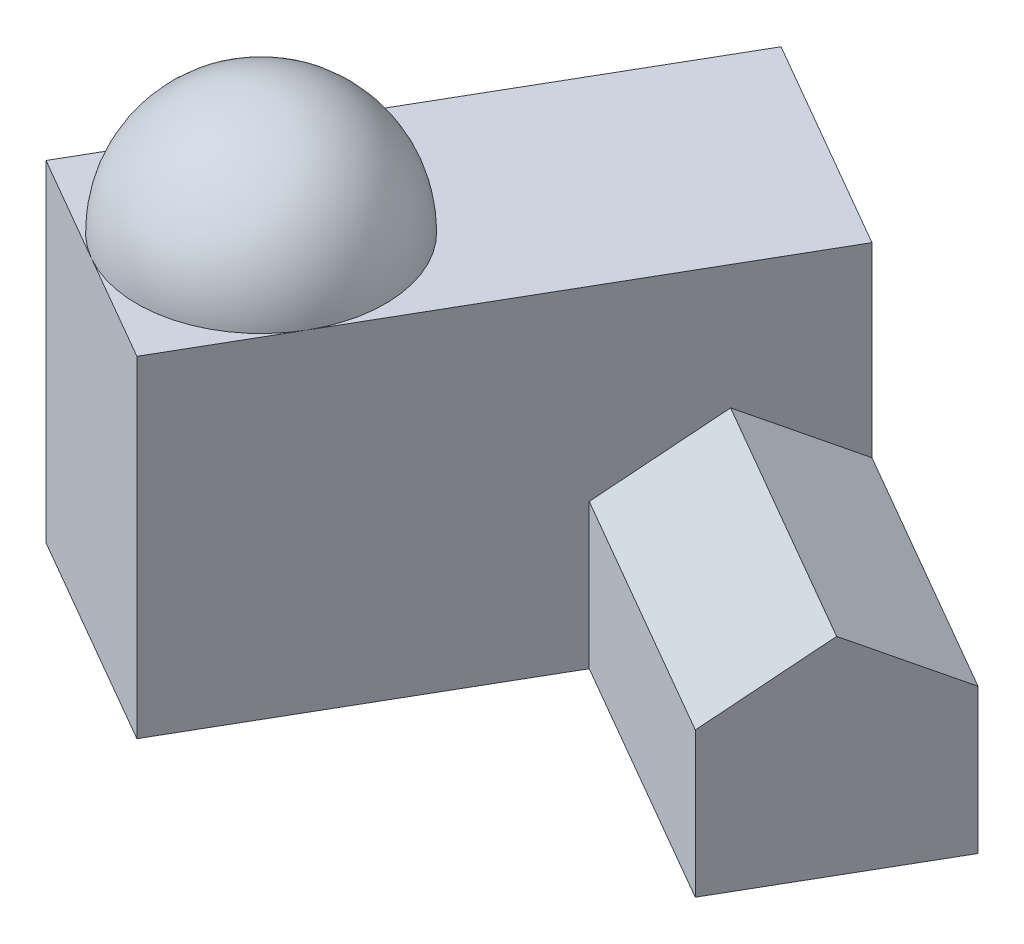
SolidWorks part; units mm, degrees
ref_plane "Front" through (0, 0, 0) normal (0, 0, 1) x (1, 0, 0)
ref_plane "Top" through (0, 0, 0) normal (0, 1, 0) x (1, 0, 0)
ref_plane "Right" through (0, 0, 0) normal (1, 0, 0) x (0, 0, -1)
sketch "Sketch1" plane through (0, 0, 0) normal (0, 1, 0) x (1, 0, 0)
  line L0 (0, 0) -> (-65, -112.5833)
  line L1 (-65, -112.5833) -> (-13.0385, -142.5833)
  line L2 (-13.0385, -142.5833) -> (51.9615, -30)
  line L3 (51.9615, -30) -> (0, 0)
  line L4 (0, 0) -> (-36.6551, 0) construction
  dimension "D1" = 60
  dimension "D2" = 130
  dimension "D3" = 60
extrude "Main Building" add sketch "Sketch1" along normal blind 80
sketch "Sketch2" plane through (0, 80, 0) normal (0, 1, 0) x (-1, 0, 0)
  line L0 (65, 112.5833) -> (13.0385, 142.5833) construction
  line L1 (13.0385, 142.5833) -> (-51.9615, 30) construction
  line L2 (0, 0) -> (65, 112.5833) construction
  line L3 (24.0192, 71.6025) -> (24.0192, 131.6025)
  arc A0 (24.0192, 131.6025) -> (24.0192, 71.6025) centre (24.0192, 101.6025) ccw
revolve "Dome" add sketch "Sketch2" angle 360 about L3
sketch "Sketch3" plane through (0, 0, 0) normal (0, 1, 0) x (1, 0, 0)
  line L0 (51.9615, -30) -> (112.5833, -65)
  line L1 (112.5833, -65) -> (87.5833, -108.3013)
  line L2 (87.5833, -108.3013) -> (26.9615, -73.3013)
  line L3 (1.9615, -116.6025) -> (51.9615, -30) construction
  line L4 (26.9615, -73.3013) -> (51.9615, -30)
  line L5 (51.9615, -30) -> (0, 0) construction
  dimension "D1" = 70
  dimension "D2" = 50
extrude "Small Building" add sketch "Sketch3" along normal blind 35
sketch "Sketch4" plane through (112.5833, 0, 65) normal (0.866, 0, 0.5) x (0.5, 0, -0.866)
  line L0 (0, 35) -> (-50, 35)
  line L1 (-50, 35) -> (-25, 50)
  line L2 (-25, 50) -> (0, 35)
  dimension "D1" = 15
extrude "Small Building Roof" add sketch "Sketch4" against normal blind 70
